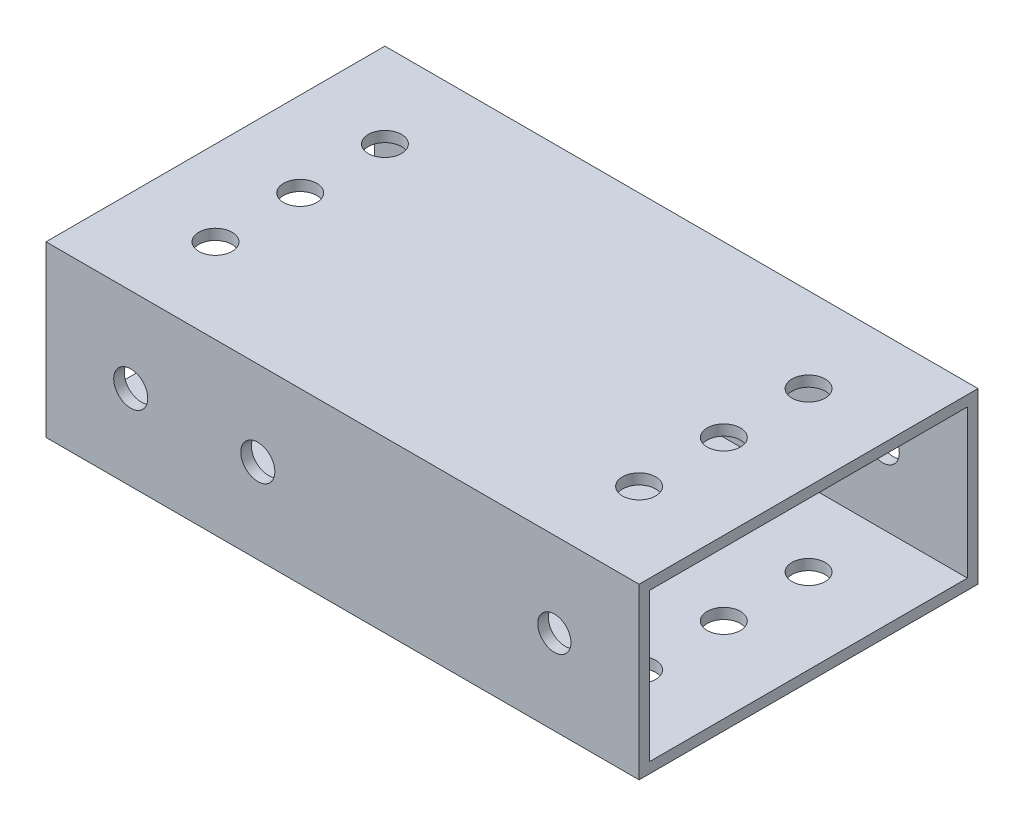
SolidWorks part; units mm, degrees
material "6061-T6 (SS)"
ref_plane "Front Plane" through (0, 0, 0) normal (0, 0, 1) x (1, 0, 0)
ref_plane "Top Plane" through (0, 0, 0) normal (0, 1, 0) x (1, 0, 0)
ref_plane "Right Plane" through (0, 0, 0) normal (1, 0, 0) x (0, 0, -1)
sketch "Sketch1" plane through (0, 0, 0) normal (1, 0, 0) x (0, 0, -1)
  line L1 (0, 0) -> (50.8, 0)
  line L2 (0, 0) -> (0, 25.4)
  line L3 (0, 25.4) -> (50.8, 25.4)
  line L4 (50.8, 0) -> (50.8, 25.4)
  dimension "D1" = 25.4
  dimension "D2" = 50.8
extrude "Boss-Extrude1" add sketch "Sketch1" along normal mid plane 88.9
shell "Shell1" thickness 1.5875
sketch "Sketch2" plane through (0, 25.4, 0) normal (0, 1, 0) x (1, 0, 0)
  line L0 (-31.75, 50.8) -> (-31.75, 0) construction
  line L1 (44.45, 50.8) -> (-44.45, 50.8) construction
  line L2 (44.45, 0) -> (-44.45, 0) construction
  line L3 (-44.45, 50.8) -> (-44.45, 0) construction
  circle A0 centre (-31.75, 25.4) radius 2.4892
  circle A1 centre (-31.75, 12.7) radius 2.4892
  circle A2 centre (-31.75, 38.1) radius 2.4892
  dimension "D1" = 4.9784
  dimension "D2" = 12.7
  dimension "D3" = 12.7
  dimension "D4" = 12.7
extrude "Cut-Extrude1" cut sketch "Sketch2" against normal through all
sketch "Sketch3" plane through (0, 0, 0) normal (0, 0, 1) x (1, 0, 0)
  line L0 (44.45, 25.4) -> (-44.45, 25.4) construction
  line L1 (-44.45, 25.4) -> (-44.45, 0) construction
  circle A0 centre (-31.75, 12.7) radius 2.4892
  dimension "D3" = 4.9784
  dimension "D1" = 12.7
  dimension "D2" = 12.7
extrude "Cut-Extrude2" cut sketch "Sketch3" against normal through all
mirror "Mirror1" about plane through (0, 0, 0) normal (1, 0, 0) of "Cut-Extrude2", "Cut-Extrude1"
sketch "Sketch4" plane through (0, 0, 0) normal (0, 0, 1) x (1, 0, 0)
  line L0 (-44.45, 25.4) -> (-44.45, 0) construction
  circle A0 centre (-12.7, 12.7) radius 2.5527
  circle A1 centre (-31.75, 12.7) radius 2.4892 construction
  point P5 (-44.45, 12.7)
  dimension "D1" = 19.05
  dimension "D2" = 5.1054
extrude "Cut-Extrude3" cut sketch "Sketch4" against normal through all
sketch "Sketch5" plane through (0, 0, 0) normal (0, 0, 1) x (1, 0, 0)
  circle A0 centre (-31.75, 12.7) radius 2.5527
  circle A1 centre (-12.7, 12.7) radius 2.5527 construction
extrude "Cut-Extrude4" cut sketch "Sketch5" against normal up to next
